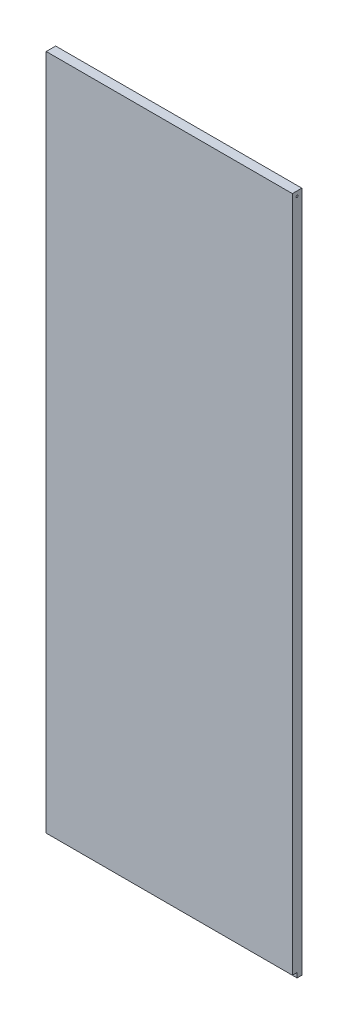
SolidWorks part; units mm, degrees
ref_plane "Front Plane" through (0, 0, 0) normal (0, 0, 1) x (1, 0, 0)
ref_plane "Top Plane" through (0, 0, 0) normal (0, 1, 0) x (1, 0, 0)
ref_plane "Right Plane" through (0, 0, 0) normal (1, 0, 0) x (0, 0, -1)
sketch "Sketch1" plane through (0, 0, 0) normal (0, 0, 1) x (1, 0, 0)
  line L1 (0, 0) -> (317.5, 0)
  line L5 (-6.35, 419.1) -> (-6.35, 914.4)
  line L7 (158.75, 914.4) -> (158.75, 50914.4) construction
  line L10 (323.85, 419.1) -> (323.85, 914.4)
  line L11 (-6.35, 914.4) -> (323.85, 914.4)
  line L12 (-6.35, 419.1) -> (-6.35, 0)
  line L13 (-6.35, 0) -> (0, 0)
  line L14 (323.85, 419.1) -> (323.85, 0)
  line L15 (323.85, 0) -> (317.5, 0)
  dimension "D1" = 317.5
  dimension "D2" = 914.4
extrude "Boss-Extrude1" add sketch "Sketch1" along normal blind 12.7
sketch "Sketch2" plane through (0, 0, 12.7) normal (0, 0, 1) x (1, 0, 0)
  line L7 (-6.35, 914.4) -> (-6.35, 0) construction
  line L8 (-6.35, 6.35) -> (323.85, 6.35)
  line L9 (-6.35, 6.35) -> (-6.35, 0)
  line L10 (-6.35, 0) -> (323.85, 0)
  line L11 (323.85, 6.35) -> (323.85, 0)
  dimension "D1" = 6.35
extrude "Cut-Extrude1" cut sketch "Sketch2" against normal blind 6.35
sketch "Sketch3" plane through (-6.35, 0, 0) normal (-1, 0, 0) x (0, 0, 1)
  line L0 (12.7, 914.4) -> (12.7, 6.35) construction
  line L1 (12.7, 914.4) -> (0, 914.4) construction
  circle A0 centre (6.35, 908.05) radius 1.27
  dimension "D1" = 2.54
  dimension "D2" = 6.35
  dimension "D3" = 6.35
extrude "Cut-Extrude2" cut sketch "Sketch3" against normal through all
